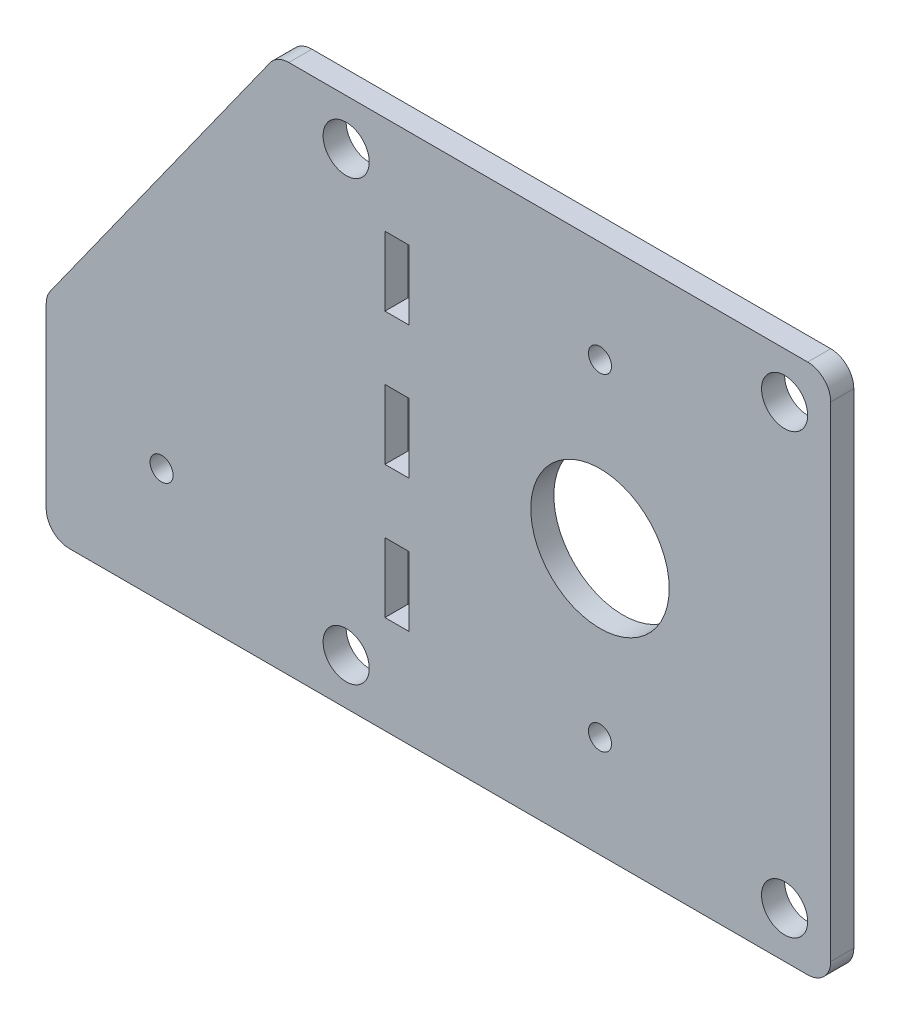
SolidWorks part; units mm, degrees
ref_plane "Front Plane" through (0, 0, 0) normal (0, 0, 1) x (1, 0, 0)
ref_plane "Top Plane" through (0, 0, 0) normal (0, 1, 0) x (1, 0, 0)
ref_plane "Right Plane" through (0, 0, 0) normal (1, 0, 0) x (0, 0, -1)
sketch "Sketch1" plane through (0, 0, 0) normal (0, 0, 1) x (1, 0, 0)
  line L0 (0, 73.025) -> (0, -73.025) construction
  line L1 (63.5, 73.025) -> (-152.4, 73.025)
  line L2 (63.5, 73.025) -> (63.5, -73.025)
  line L3 (63.5, -73.025) -> (-152.4, -73.025)
  line L4 (-152.4, 73.025) -> (-152.4, -73.025)
  line L5 (0, 45) -> (0, -45) construction
  line L6 (-55.88, 73.025) -> (-55.88, 36.5125) construction
  line L7 (-59.182, -9.525) -> (-52.578, -9.525)
  line L8 (-59.182, -9.525) -> (-59.182, 9.525)
  line L9 (-59.182, 9.525) -> (-52.578, 9.525)
  line L10 (-52.578, -9.525) -> (-52.578, 9.525)
  line L11 (-59.182, -9.525) -> (-52.578, 9.525) construction
  line L12 (-59.182, 9.525) -> (-52.578, -9.525) construction
  line L13 (-59.182, 46.0375) -> (-52.578, 46.0375)
  line L14 (-59.182, 46.0375) -> (-59.182, 26.9875)
  line L15 (-59.182, 26.9875) -> (-52.578, 26.9875)
  line L16 (-52.578, 46.0375) -> (-52.578, 26.9875)
  line L17 (-59.182, 46.0375) -> (-52.578, 26.9875) construction
  line L18 (-59.182, 26.9875) -> (-52.578, 46.0375) construction
  line L19 (-59.182, -26.9875) -> (-52.578, -26.9875)
  line L20 (-59.182, -26.9875) -> (-59.182, -46.0375)
  line L21 (-59.182, -46.0375) -> (-52.578, -46.0375)
  line L22 (-52.578, -26.9875) -> (-52.578, -46.0375)
  line L23 (-59.182, -26.9875) -> (-52.578, -46.0375) construction
  line L24 (-59.182, -46.0375) -> (-52.578, -26.9875) construction
  line L25 (-55.88, 36.5125) -> (-55.88, 0) construction
  line L26 (-55.88, 0) -> (-55.88, -36.5125) construction
  line L27 (-55.88, -36.5125) -> (-55.88, -73.025) construction
  circle A0 centre (50.8, 60.325) radius 6.35
  circle A1 centre (50.8, -60.325) radius 6.35
  circle A2 centre (0, 0) radius 19.05
  circle A3 centre (0, 45) radius 3.175
  circle A4 centre (0, -45) radius 3.175
  circle A5 centre (-69.85, 60.325) radius 6.35
  circle A6 centre (-69.85, -60.325) radius 6.35
  point P0 (0, 0)
  point P14 (0, 0)
  point P19 (0, 0)
  point P24 (-55.88, 36.5125)
  point P28 (-55.88, 0)
  point P34 (-55.88, -36.5125)
  dimension "D2" = 12.7
  dimension "D6" = 38.1
  dimension "D8" = 6.35
  dimension "D1" = 146.05
  dimension "D3" = 12.7
  dimension "D4" = 12.7
  dimension "D5" = 50.8
  dimension "D7" = 90
  dimension "D9" = 12.7
  dimension "D10" = 152.4
  dimension "D11" = 69.85
  dimension "D12" = 19.05
  dimension "D13" = 6.604
  dimension "D14" = 55.88
extrude "Boss-Extrude1" add sketch "Sketch1" along normal mid plane 6.35
sketch "Sketch2" plane through (0, 0, 3.175) normal (0, 0, 1) x (1, 0, 0)
  line L0 (-152.4, -73.025) -> (63.5, -73.025) construction
  line L1 (-152.4, 73.025) -> (-152.4, -73.025) construction
  line L2 (-88.9, 73.025) -> (-152.4, -15.875)
  line L3 (63.5, 73.025) -> (-152.4, 73.025) construction
  line L4 (-152.4, -15.875) -> (-152.4, 73.025)
  line L5 (-152.4, 73.025) -> (-88.9, 73.025)
  circle A0 centre (-120.65, -41.275) radius 3.175
  dimension "D1" = 6.35
  dimension "D2" = 31.75
  dimension "D3" = 31.75
  dimension "D4" = 88.9
  dimension "D5" = 63.5
extrude "Cut-Extrude1" cut sketch "Sketch2" against normal through all
fillet "Fillet1" radius 6.35 5 edges at (63.5, 73.025, 0) (63.5, -73.025, 0) (-88.9, 73.025, 0) (-152.4, -15.875, 0) (-152.4, -73.025, 0)
